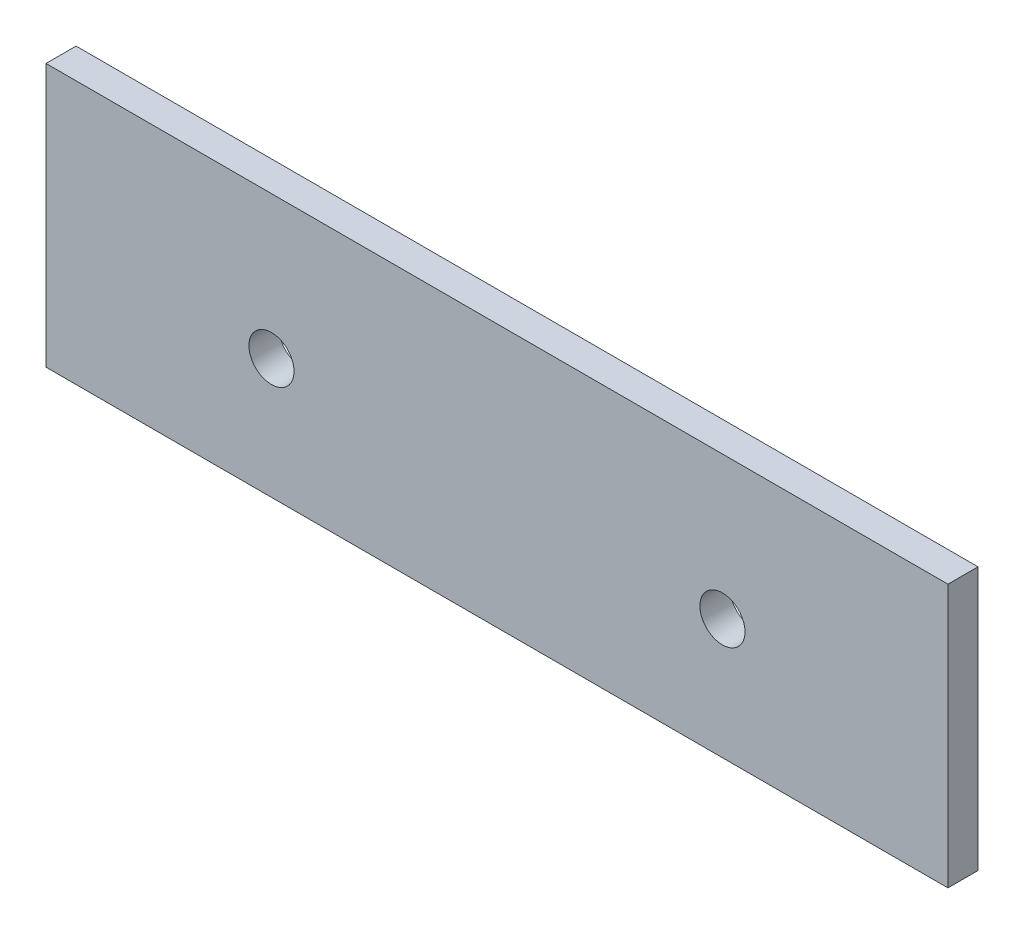
SolidWorks part; units mm, degrees
ref_plane "Alzado" through (0, 0, 0) normal (0, 0, 1) x (1, 0, 0)
ref_plane "Planta" through (0, 0, 0) normal (0, 1, 0) x (1, 0, 0)
ref_plane "Vista lateral" through (0, 0, 0) normal (1, 0, 0) x (0, 0, -1)
sketch "Croquis1" plane through (0, 0, 0) normal (0, 0, 1) x (1, 0, 0)
  line L1 (-30, -8.75) -> (30, -8.75)
  line L2 (-30, -8.75) -> (-30, 8.75)
  line L3 (-30, 8.75) -> (30, 8.75)
  line L4 (30, -8.75) -> (30, 8.75)
  line L5 (-30, -8.75) -> (30, 8.75) construction
  line L6 (-30, 8.75) -> (30, -8.75) construction
  point P0 (0, 0)
  dimension "D1" = 17.5
  dimension "D2" = 60
extrude "Saliente-Extruir1" add sketch "Croquis1" along normal blind 2
sketch "Croquis2" plane through (0, 0, 0) normal (0, 0, -1) x (-1, 0, 0)
  line L0 (-15, -0.75) -> (0, -0.75) construction
  line L1 (0, -0.75) -> (0, -8.75) construction
  line L2 (30, -8.75) -> (-30, -8.75) construction
  line L3 (-24.9942, 7.25) -> (22.0297, 7.25) construction
  line L4 (0, 7.25) -> (0, -0.75) construction
  line L5 (-30, -0.75) -> (-15, -0.75) construction
  line L6 (-30, -8.75) -> (-30, 8.75) construction
  line L7 (15, -0.75) -> (30, -0.75) construction
  line L8 (30, 8.75) -> (30, -8.75) construction
  line L9 (0, -0.75) -> (15, -0.75) construction
  circle A0 centre (15, -0.75) radius 1.5
  circle A1 centre (-15, -0.75) radius 1.5
  dimension "D2" = 3
  dimension "D1" = 16
extrude "Cortar-Extruir1" cut sketch "Croquis2" against normal through all
